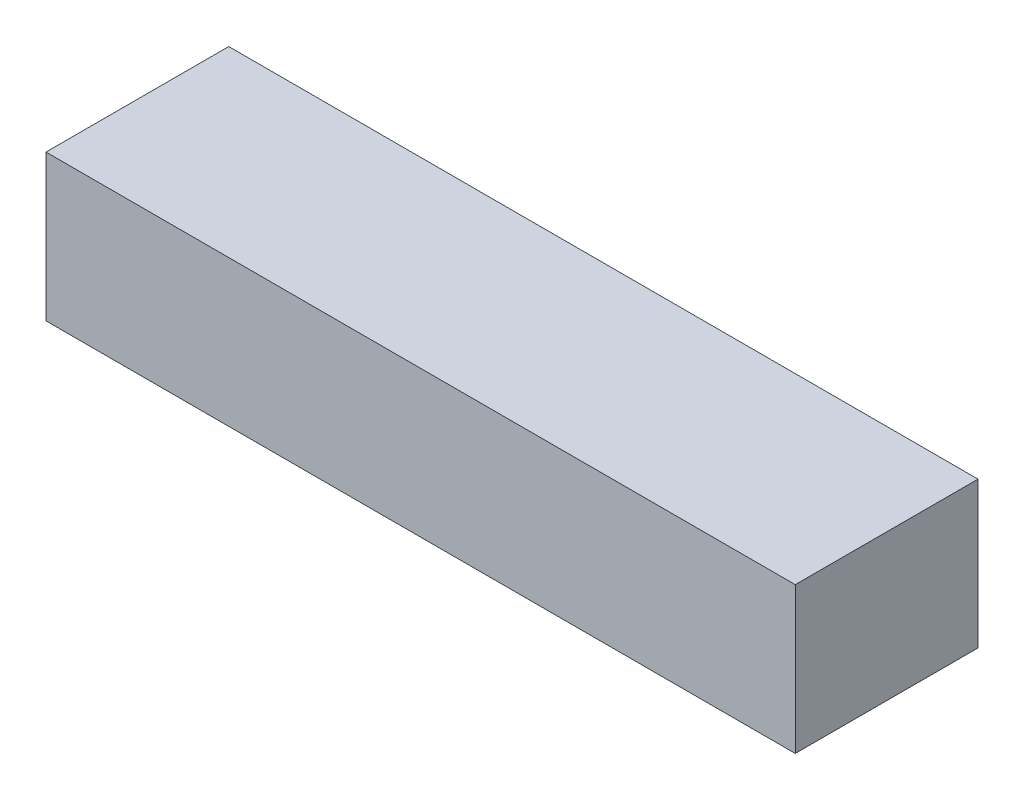
SolidWorks part; units mm, degrees
ref_plane "Front Plane" through (0, 0, 0) normal (0, 0, 1) x (1, 0, 0)
ref_plane "Top Plane" through (0, 0, 0) normal (0, 1, 0) x (1, 0, 0)
ref_plane "Right Plane" through (0, 0, 0) normal (1, 0, 0) x (0, 0, -1)
sketch "Sketch1" plane through (0, 0, 0) normal (0, 1, 0) x (1, 0, 0)
  line L1 (-65.0875, -15.875) -> (65.0875, -15.875)
  line L2 (-65.0875, -15.875) -> (-65.0875, 15.875)
  line L3 (-65.0875, 15.875) -> (65.0875, 15.875)
  line L4 (65.0875, -15.875) -> (65.0875, 15.875)
  line L5 (-65.0875, -15.875) -> (65.0875, 15.875) construction
  line L6 (-65.0875, 15.875) -> (65.0875, -15.875) construction
  point P0 (0, 0)
  dimension "D1" = 130.175
  dimension "D2" = 31.75
extrude "Boss-Extrude1" add sketch "Sketch1" along normal blind 25.4
